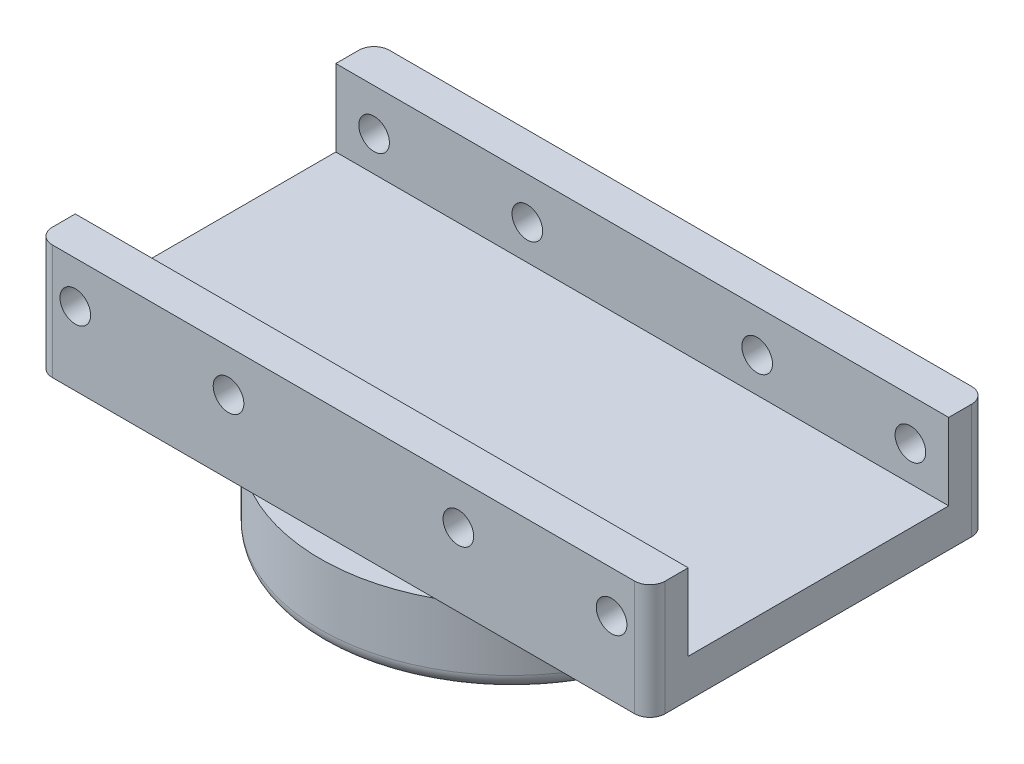
SolidWorks part; units mm, degrees
ref_plane "前基準面" through (0, 0, 0) normal (0, 0, 1) x (1, 0, 0)
ref_plane "上基準面" through (0, 0, 0) normal (0, 1, 0) x (1, 0, 0)
ref_plane "右基準面" through (0, 0, 0) normal (1, 0, 0) x (0, 0, -1)
sketch "草圖1" plane through (0, 0, 0) normal (0, 1, 0) x (1, 0, 0)
  circle A0 centre (0, 0) radius 25
  dimension "D1" = 50
extrude "填料-伸長1" add sketch "草圖1" along normal blind 10
sketch "草圖2" plane through (0, 0, 0) normal (0, -1, 0) x (1, 0, 0)
  circle A0 centre (0, 0) radius 10
  dimension "D1" = 20
extrude "填料-伸長2" add sketch "草圖2" along normal blind 10
fillet "圓角1" radius 2 2 edges at (0, -10, -10) (0, 0, 25)
sketch "草圖3" plane through (0, 10, 0) normal (0, 1, 0) x (1, 0, 0)
  line L1 (-35, -17) -> (35, -17) construction
  line L2 (-35, -17) -> (-35, 17) construction
  line L3 (-35, 17) -> (35, 17) construction
  line L4 (35, -17) -> (35, 17) construction
  line L5 (-35, -17) -> (35, 17) construction
  line L6 (-35, 17) -> (35, -17) construction
  line L7 (-40, -22) -> (40, -22)
  line L8 (-40, -22) -> (-40, 22)
  line L9 (-40, 22) -> (40, 22)
  line L10 (40, -22) -> (40, 22)
  line L11 (-40, -22) -> (40, 22) construction
  line L12 (-40, 22) -> (40, -22) construction
  point P0 (0, 0)
  point P6 (0, 0)
  dimension "D1" = 34
  dimension "D2" = 70
  dimension "D3" = 5
  dimension "D4" = 5
extrude "填料-伸長3" add sketch "草圖3" along normal blind 5
sketch "草圖4" plane through (0, 15, 0) normal (0, 1, 0) x (1, 0, 0)
  line L0 (40, -22) -> (40, 22) construction
  line L1 (-35, -17) -> (35, -17) construction
  line L2 (-35, -17) -> (-35, 17) construction
  line L3 (-35, 17) -> (35, 17) construction
  line L4 (35, -17) -> (35, 17) construction
  line L5 (-35, -17) -> (35, 17) construction
  line L6 (-35, 17) -> (35, -17) construction
  line L7 (-40, 22) -> (40, 22)
  line L8 (-40, 22) -> (-40, 17)
  line L9 (-40, 17) -> (40, 17)
  line L10 (40, 22) -> (40, 17)
  line L12 (-40, -22) -> (40, -22)
  line L13 (-40, -22) -> (-40, -17)
  line L14 (-40, -17) -> (40, -17)
  line L15 (40, -22) -> (40, -17)
  point P0 (0, 0)
  dimension "D1" = 34
  dimension "D2" = 70
extrude "填料-伸長4" add sketch "草圖4" along normal blind 10
sketch "草圖5" plane through (0, 0, -22) normal (0, 0, -1) x (-1, 0, 0)
  line L0 (0, 28.518) -> (0, 0) construction
  line L1 (-40, 25) -> (-40, 15) construction
  line L2 (-40, 15) -> (-40, 19.5451) construction
  line L3 (-40, 19.5451) -> (40, 19.5451) construction
  line L4 (40, 25) -> (40, 10) construction
  circle A0 centre (-15, 19.5451) radius 2
  circle A1 centre (-35, 19.5451) radius 2
  circle A2 centre (15, 19.5451) radius 2
  circle A3 centre (35, 19.5451) radius 2
  dimension "D1" = 4
  dimension "D2" = 15
  dimension "D3" = 35
extrude "除料-伸長1" cut sketch "草圖5" against normal blind 81
fillet "圓角4" radius 2 4 edges at (-40, 17.5, -22) (-40, 17.5, 22) (40, 17.5, -22) (40, 17.5, 22)
